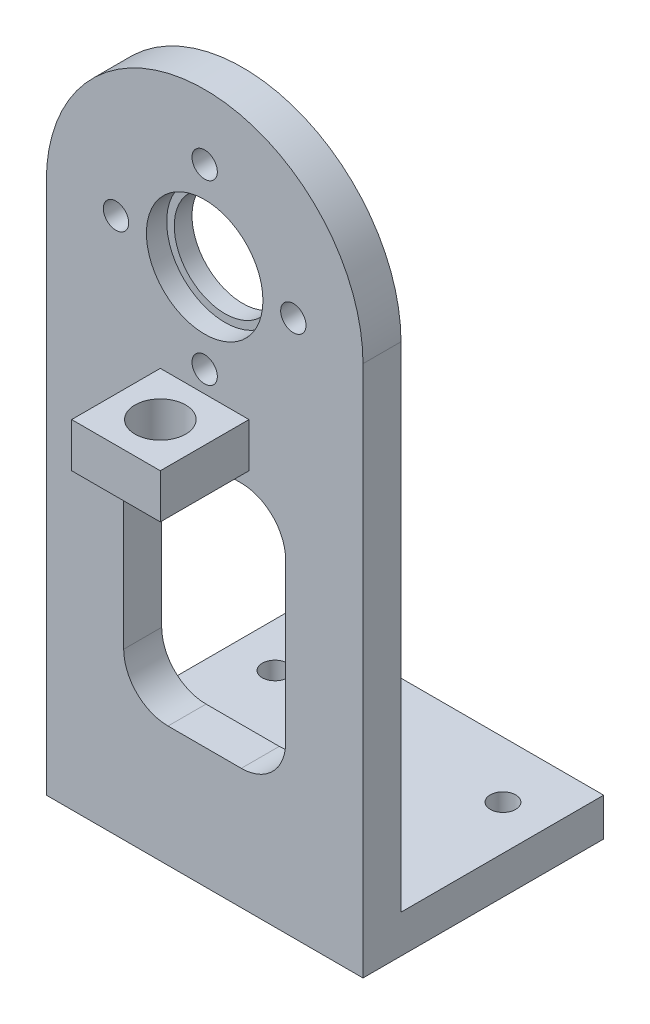
SolidWorks part; units mm, degrees
material "ABS"
ref_plane "Front Plane" through (0, 0, 0) normal (0, 0, 1) x (1, 0, 0)
ref_plane "Top Plane" through (0, 0, 0) normal (0, 1, 0) x (1, 0, 0)
ref_plane "Right Plane" through (0, 0, 0) normal (1, 0, 0) x (0, 0, -1)
sketch "Sketch1" plane through (0, 0, 0) normal (0, 0, 1) x (1, 0, 0)
  line L0 (-12.5, -11.1228) -> (12.5, -11.1228)
  line L1 (-12.5, 27.4354) -> (12.5, 27.4354)
  line L2 (-12.5, 27.4354) -> (-12.5, -14.5646)
  line L3 (-12.5, -14.5646) -> (12.5, -14.5646)
  line L4 (12.5, 27.4354) -> (12.5, -14.5646)
  arc A0 (12.5, 27.4354) -> (-12.5, 27.4354) centre (0, 27.4354) ccw
  point P0 (0, 0)
  dimension "D2" = 3.4418
  dimension "D1" = 25
  dimension "D3" = 42
extrude "Boss-Extrude1" add sketch "Sketch1" along normal blind 3 contours L4 L1 L2 L0 | L1 A0 | L4 L0 L2 L3
sketch "Sketch2" plane through (0, 0, 3) normal (0, 0, 1) x (1, 0, 0)
  circle A0 centre (0, 27.802) radius 4.6
  circle A1 centre (0, 27.802) radius 4
  circle A2 centre (0, 27.802) radius 7
  circle A3 centre (0, 34.802) radius 1
  circle A4 centre (7, 27.802) radius 1
  circle A5 centre (0, 20.802) radius 1
  circle A6 centre (-7, 27.802) radius 1
  dimension "D1" = 2
  dimension "D2" = 2
  dimension "D3" = 2
  dimension "D4" = 2
  dimension "D5" = 8
  dimension "D6" = 9.2
  dimension "D7" = 14
extrude "Cut-Extrude1" cut sketch "Sketch2" against normal blind 3 contours A2 A4 | A2 A4 | A2 A3 | A2 A3 | A2 A6 | A2 A6 | A2 A5 | A1
sketch "Sketch4" plane through (0, 0, 3) normal (0, 0, 1) x (1, 0, 0)
  circle A0 centre (0, 27.802) radius 4.6
  dimension "D1" = 9.2
extrude "Cut-Extrude2" cut sketch "Sketch4" against normal blind 1.6 contours A0
sketch "Sketch5" plane through (0, 0, 3) normal (0, 0, 1) x (1, 0, 0)
  line L0 (-12.5, -11.5646) -> (12.5, -11.5646)
  line L1 (-12.5, 27.4354) -> (-12.5, -14.5646) construction
  line L2 (12.5, 27.4354) -> (12.5, -14.5646) construction
  line L3 (-12.5, -14.5646) -> (12.5, -14.5646) construction
  line L7 (12.5, -14.5646) -> (12.5, 27.4354)
  line L8 (-12.5, 27.4354) -> (-12.5, -14.5646)
  line L9 (-12.5, -14.5646) -> (12.5, -14.5646)
  line L10 (12.5, -14.5646) -> (12.5, -11.5646)
  line L11 (-12.5, -11.5646) -> (-12.5, -14.5646)
  line L12 (-12.5, -14.5646) -> (12.5, -14.5646)
  arc A1 (12.5, 27.4354) -> (-12.5, 27.4354) centre (0, 27.4354) ccw
  dimension "D1" = 3
  dimension "D2" = 0
extrude "Boss-Extrude3" add sketch "Sketch5" against normal blind 19 contours L0 L10 L12 L11
sketch "Sketch7" plane through (0, -11.5646, 0) normal (0, 1, 0) x (1, 0, 0)
  line L0 (12.5, 16) -> (12.5, 0) construction
  line L1 (-12.5, 16) -> (-12.5, 0) construction
  line L2 (-12.5, 0) -> (12.5, 0) construction
  circle A0 centre (9, 11.55) radius 1
  circle A1 centre (-9, 11.55) radius 1
  dimension "D3" = 2
  dimension "D4" = 2
  dimension "D1" = 3.5
  dimension "D2" = 3.5
  dimension "D5" = 11.55
  dimension "D6" = 11.55
extrude "Cut-Extrude4" cut sketch "Sketch7" against normal blind 4
sketch "Sketch8" plane through (0, 0, 3) normal (0, 0, 1) x (1, 0, 0)
  line L1 (-6.3919, 14.467) -> (6.3919, 14.467)
  line L2 (-6.3919, 14.467) -> (-6.3919, -5.033)
  line L3 (-6.3919, -5.033) -> (6.3919, -5.033)
  line L4 (6.3919, 14.467) -> (6.3919, -5.033)
  point P0 (0, 4.717)
  dimension "D1" = 19.5
extrude "Cut-Extrude5" cut sketch "Sketch8" against normal blind 4 contours L4 L1 L2 L3
fillet "Fillet1" radius 3.5 4 edges at (-6.3919, -5.033, 1.5) (6.3919, -5.033, 1.5) (6.3919, 14.467, 1.5) (-6.3919, 14.467, 1.5)
sketch "Sketch9" plane through (0, 0, 3) normal (0, 0, 1) x (1, 0, 0)
  line L0 (12.5, 27.4354) -> (12.5, -14.5646) construction
  line L1 (-3.5, 15.6154) -> (3.5, 15.6154)
  line L2 (-3.5, 15.6154) -> (-3.5, 19.1154)
  line L3 (-3.5, 19.1154) -> (3.5, 19.1154)
  line L4 (3.5, 15.6154) -> (3.5, 19.1154)
  line L5 (-3.5, 15.6154) -> (3.5, 19.1154) construction
  line L6 (-3.5, 19.1154) -> (3.5, 15.6154) construction
  line L7 (-12.5, -14.5646) -> (12.5, -14.5646) construction
  point P0 (0, 17.3654)
  dimension "D1" = 7
  dimension "D2" = 3.5
  dimension "D3" = 12.5
  dimension "D4" = 31.93
extrude "Boss-Extrude4" add sketch "Sketch9" along normal blind 7
sketch "Sketch10" plane through (0, 19.1154, 0) normal (0, 1, 0) x (1, 0, 0)
  line L0 (3.5, -10) -> (-3.5, -10) construction
  line L1 (-3.5, -10) -> (-3.5, -3) construction
  circle A0 centre (0, -6.5) radius 2
  dimension "D3" = 4
  dimension "D1" = 3.5
  dimension "D2" = 3.5
extrude "Cut-Extrude6" cut sketch "Sketch10" against normal blind 7 contours A0
